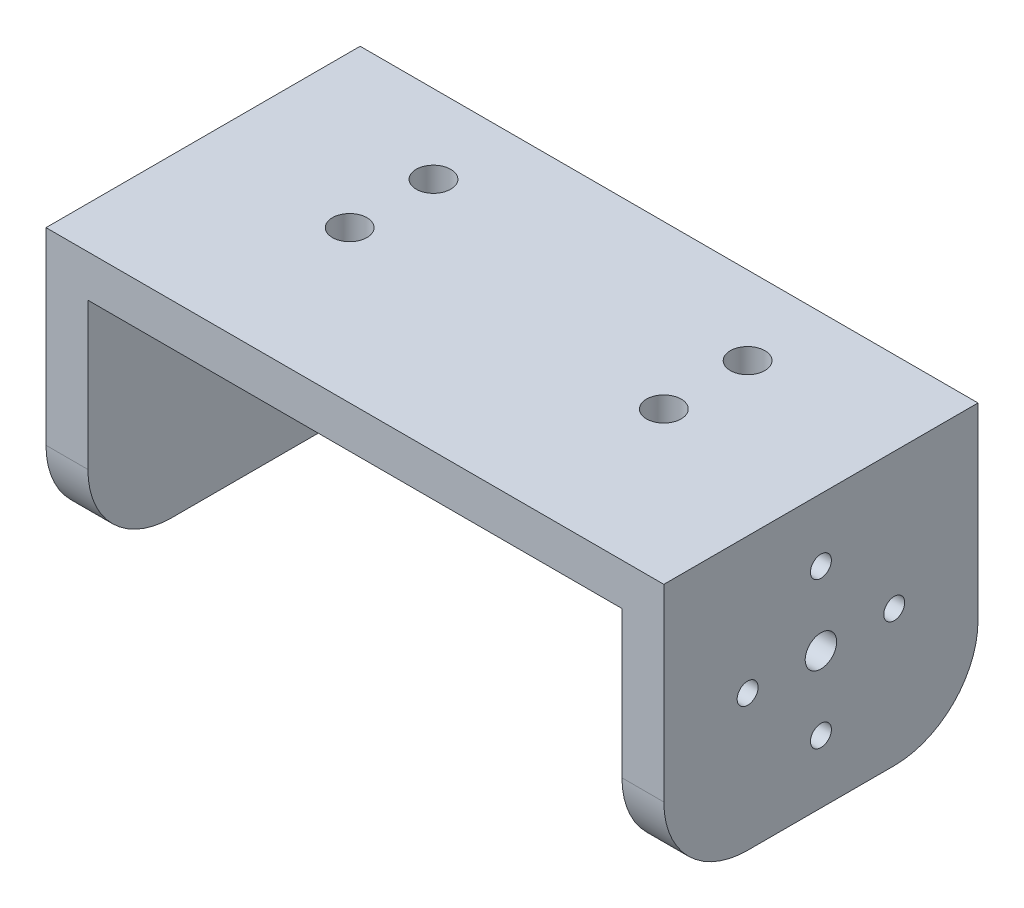
SolidWorks part; units mm, degrees
ref_plane "前视基准面" through (0, 0, 0) normal (0, 0, 1) x (1, 0, 0)
ref_plane "上视基准面" through (0, 0, 0) normal (0, 1, 0) x (1, 0, 0)
ref_plane "右视基准面" through (0, 0, 0) normal (1, 0, 0) x (0, 0, -1)
sketch "草图1" plane through (0, 0, 0) normal (0, 0, 1) x (1, 0, 0)
  line L0 (0, 0) -> (29.5, 0)
  line L1 (29.5, 0) -> (29.5, -26)
  line L2 (0, -4) -> (25.5, -4)
  line L3 (25.5, -4) -> (25.5, -26)
  line L4 (25.5, -26) -> (29.5, -26)
  line L5 (0, 0) -> (0, -6.7603) construction
  line L6 (-25.5, -26) -> (-29.5, -26)
  line L7 (-29.5, 0) -> (-29.5, -26)
  line L8 (-25.5, -4) -> (-25.5, -26)
  line L9 (0, -4) -> (-25.5, -4)
  line L10 (0, 0) -> (-29.5, 0)
  dimension "D1" = 29.5
  dimension "D3" = 26
  dimension "D2" = 4
extrude "凸台-拉伸1" add sketch "草图1" along normal blind 30
sketch "草图3" plane through (29.5, 0, 0) normal (1, 0, 0) x (0, 0, -1)
  line L3 (-30, -13) -> (-15, -13) construction
  line L5 (-30, -26) -> (-30, 0) construction
  line L6 (-15, -13) -> (0, -13) construction
  line L9 (0, -26) -> (0, 0) construction
  circle A0 centre (-15, -13) radius 10
  dimension "D1" = 20
fillet "圆角1" radius 8 4 edges at (-27.5, -26, 30) (-27.5, -26, 0) (27.5, -26, 0) (27.5, -26, 30)
sketch "草图4" plane through (0, 0, 0) normal (0, 1, 0) x (1, 0, 0)
  line L0 (0, 0) -> (0, -31.9875) construction
  line L1 (29.5, 0) -> (-29.5, 0) construction
  line L2 (-15, -7.5) -> (15, -7.5) construction
  line L3 (23.4432, -11.5) -> (-25.098, -11.5) construction
  circle A0 centre (15, -7.5) radius 1.65
  circle A1 centre (-15, -7.5) radius 1.65
  circle A2 centre (-15, -15.5) radius 1.65
  circle A3 centre (15, -15.5) radius 1.65
  dimension "D1" = 3.3
  dimension "D2" = 15
  dimension "D3" = 7.5
  dimension "D4" = 11.5
extrude "切除-拉伸1" cut sketch "草图4" against normal blind 10
sketch "草图5" plane through (-29.5, 0, 0) normal (-1, 0, 0) x (0, 0, 1)
  circle A0 centre (15, -13) radius 10 construction
  circle A1 centre (15, -13) radius 10 construction
  circle A2 centre (15, -13) radius 1.65
  dimension "D1" = 3.3
extrude "切除-拉伸2" cut sketch "草图5" against normal blind 10
sketch "草图6" plane through (29.5, 0, 0) normal (1, 0, 0) x (0, 0, -1)
  line L0 (-15, -13) -> (-15, -6) construction
  line L1 (-15, -13) -> (-15, -20) construction
  line L2 (-22, -13) -> (-8, -13) construction
  line L3 (-30, -13) -> (-15, -13) construction
  line L4 (-15, -13) -> (0, -13) construction
  circle A0 centre (-15, -13) radius 7 construction
  circle A1 centre (-15, -6) radius 1
  circle A2 centre (-8, -13) radius 1
  circle A3 centre (-15, -20) radius 1
  circle A4 centre (-22, -13) radius 1
  dimension "D1" = 14
  dimension "D2" = 2
extrude "切除-拉伸3" cut sketch "草图6" against normal blind 10
sketch "草图7" plane through (29.5, 0, 0) normal (1, 0, 0) x (0, 0, -1)
  circle A0 centre (-15, -13) radius 1.5
  dimension "D1" = 3
extrude "切除-拉伸4" cut sketch "草图7" against normal blind 10
